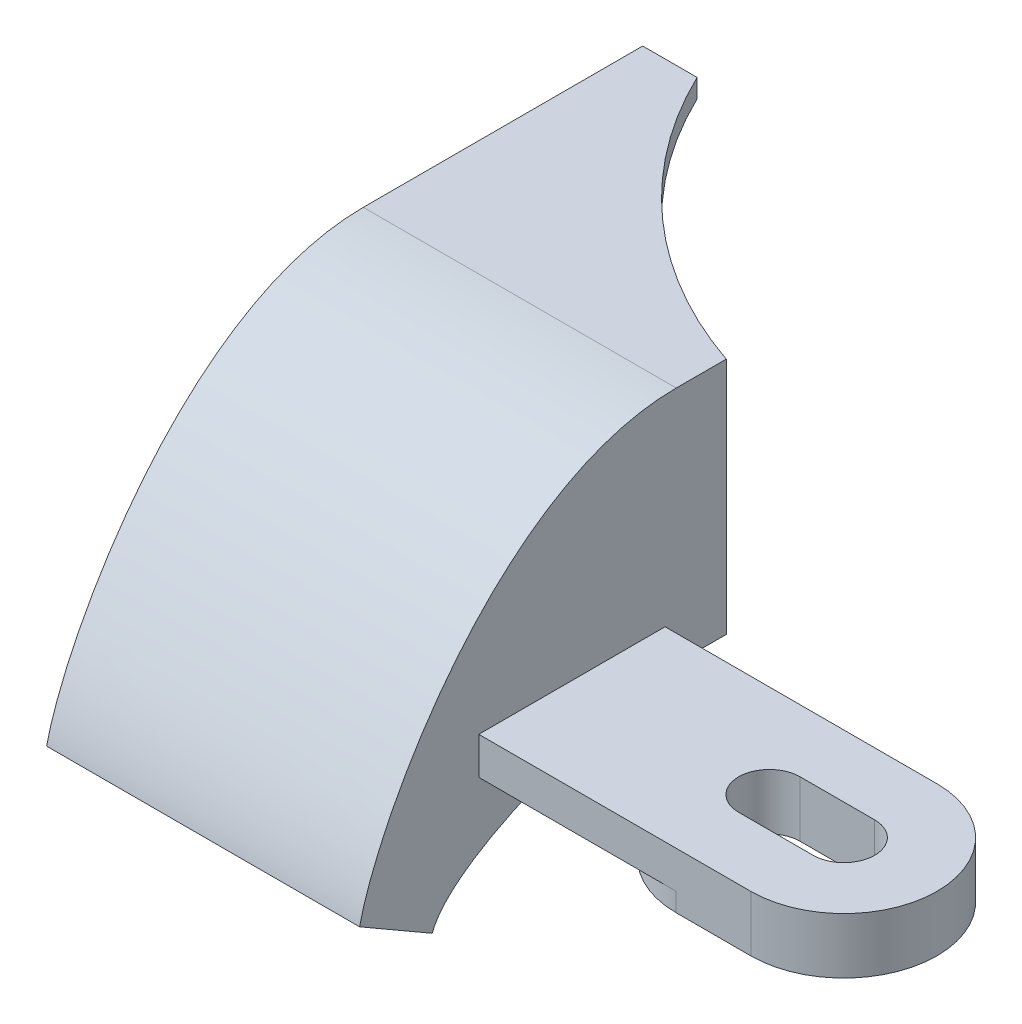
SolidWorks part; units mm, degrees
ref_plane "Plano frontal" through (0, 0, 0) normal (0, 0, 1) x (1, 0, 0)
ref_plane "Plano superior" through (0, 0, 0) normal (0, 1, 0) x (1, 0, 0)
ref_plane "Plano direito" through (0, 0, 0) normal (1, 0, 0) x (0, 0, -1)
sketch "Esboço1" plane through (0, 0, 0) normal (0, 0, 1) x (1, 0, 0)
  line L1 (-8.4, 6.4) -> (8.4, 6.4)
  line L2 (-8.4, 6.4) -> (-8.4, -6.4)
  line L3 (-8.4, -6.4) -> (8.4, -6.4)
  line L4 (8.4, 6.4) -> (8.4, -6.4)
  line L5 (-8.4, 6.4) -> (8.4, -6.4) construction
  line L6 (-8.4, -6.4) -> (8.4, 6.4) construction
  point P0 (0, 0)
  dimension "D1" = 12.8
  dimension "D2" = 16.8
extrude "Ressalto-extrusão1" add sketch "Esboço1" along normal blind 15
sketch "Esboço2" plane through (8.4, 0, 0) normal (1, 0, 0) x (0, 0, -1)
  line L0 (-15, -6.4) -> (0, -6.4) construction
  line L1 (-18.6376, -6.4) -> (-11.3604, -6.4) construction
  line L2 (-28.1029, -12.4) -> (-32, -10.15)
  line L3 (-15, 6.4) -> (-15, -6.4)
  line L6 (-15, 6.4) -> (0, 6.4) construction
  line L7 (-21.1788, 6.4) -> (-8.8176, 6.4) construction
  spline S0 degree 3 poles (-15, 6.4) (-24.57, 6.4) (-31.0693, -5.7492) (-32, -10.15) knots 0 0 0 0 1 1 1 1
  spline S1 degree 3 poles (-15, -6.4) (-18.0322, -6.4) (-26.9448, -9.2979) (-28.1029, -12.4) knots 0 0 0 0 1 1 1 1
  dimension "D1" = 17
  dimension "D2" = 6
  dimension "D3" = 4.5
  dimension "D4" = 30
extrude "Ressalto-extrusão2" add sketch "Esboço2" against normal through all
shell "Casca1" thickness 1
sketch "Esboço5" plane through (0, 6.4, 0) normal (0, 1, 0) x (1, 0, 0)
  circle A0 centre (16.15, 10.4) radius 24
  dimension "D1" = 48
  dimension "D2" = 7.75
  dimension "D3" = 10.4
extrude "Corte-extrusão1" cut sketch "Esboço5" against normal through all
sketch "Esboço6" plane through (0, -6.4, 0) normal (0, -1, 0) x (1, 0, 0)
  line L0 (23, 25.6) -> (8.4, 25.6)
  line L1 (8.4, 15) -> (8.4, 32) construction
  line L2 (8.4, 25.6) -> (8.4, 15.6)
  line L3 (8.4, 15.6) -> (23, 15.6)
  line L4 (19, 22.25) -> (23, 22.25)
  line L6 (19, 18.95) -> (23, 18.95)
  arc A0 (23, 18.95) -> (23, 22.25) centre (23, 20.6) ccw
  arc A1 (23, 15.6) -> (23, 25.6) centre (23, 20.6) ccw
  arc A2 (19, 22.25) -> (19, 18.95) centre (19, 20.6) ccw
  dimension "D1" = 3.3
  dimension "D4" = 5
  dimension "D2" = 20.6
  dimension "D3" = 23
  dimension "D5" = 4
extrude "Ressalto-extrusão3" add sketch "Esboço6" against normal blind 2
sketch "Esboço7" plane through (0, -6.4, 0) normal (0, -1, 0) x (1, 0, 0)
  line L0 (19, 18.95) -> (23, 18.95) construction
  line L1 (23, 22.25) -> (19, 22.25) construction
  line L2 (19, 18.95) -> (23, 18.95)
  line L3 (23, 22.25) -> (19, 22.25)
  line L4 (19, 20.6) -> (23, 20.6) construction
  line L5 (19, 25.6) -> (23, 25.6)
  line L6 (19, 15.6) -> (23, 15.6)
  arc A0 (19, 22.25) -> (19, 18.95) centre (19, 20.6) ccw construction
  arc A1 (23, 18.95) -> (23, 22.25) centre (23, 20.6) ccw construction
  arc A5 (19, 22.25) -> (19, 18.95) centre (19, 20.6) ccw
  arc A6 (23, 18.95) -> (23, 22.25) centre (23, 20.6) ccw
  arc A7 (19, 25.6) -> (19, 15.6) centre (19, 20.6) ccw
  arc A8 (23, 15.6) -> (23, 25.6) centre (23, 20.6) ccw
  arc A9 (23, 15.6) -> (23, 25.6) centre (23, 20.6) ccw construction
  point P6 (21, 20.6)
extrude "Ressalto-extrusão4" add sketch "Esboço7" along normal blind 1
